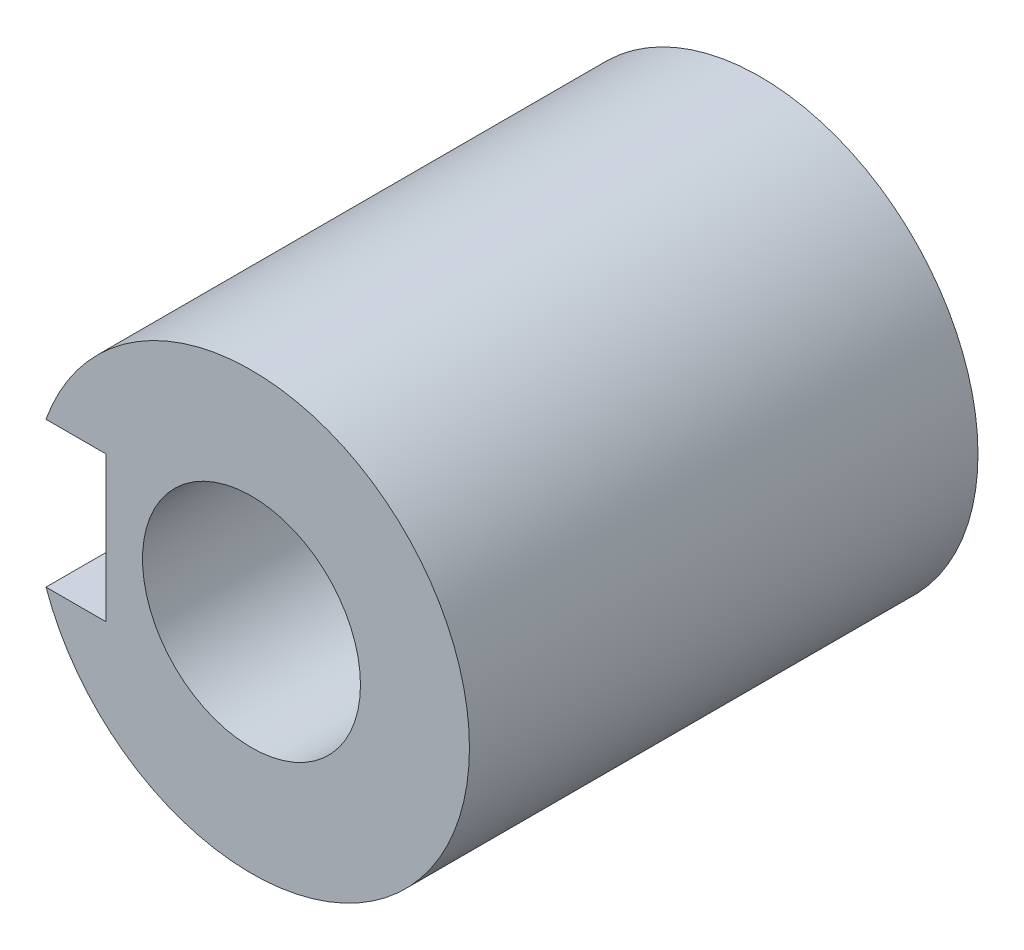
SolidWorks part; units mm, degrees
material "AISI 1020"
ref_plane "Спереди" through (0, 0, 0) normal (0, 0, 1) x (1, 0, 0)
ref_plane "Сверху" through (0, 0, 0) normal (0, 1, 0) x (1, 0, 0)
ref_plane "Справа" through (0, 0, 0) normal (1, 0, 0) x (0, 0, -1)
sketch "Эскиз1" plane through (0, 0, -1) normal (0, 0, -1) x (-1, 0, 0)
  line L0 (12, 4) -> (12, -4) construction
  line L1 (11.3137, 4) -> (8, 4)
  line L3 (11.3137, -4) -> (8, -4)
  line L4 (8, 4) -> (8, -4)
  line L5 (16, -4) -> (11.3137, -4) construction
  line L6 (11.3137, 4) -> (16, 4) construction
  arc A0 (11.3137, 4) -> (11.3137, -4) centre (0, 0) ccw
  arc A1 (11.3137, 4) -> (11.3137, -4) centre (0, 0) ccw construction
  point P6 (0, 0)
  point P15 (12, 0)
  point P17 (0, 0)
  dimension "D1" = 8
extrude "Бобышка-Вытянуть1" add sketch "Эскиз1" against normal up to surface (28 mm away)
sketch "Эскиз2" plane through (0, 0, -1) normal (0, 0, -1) x (-1, 0, 0)
  line L0 (-3.3166, 5) -> (3.3166, 5) construction
  line L1 (-3.3166, 5) -> (3.3166, 5)
  line L2 (-6, 0.6585) -> (-6, -0.6585)
  line L3 (-3.3166, -5) -> (3.3166, -5)
  line L5 (3.3166, -5) -> (-3.3166, -5) construction
  line L6 (6, 0.6585) -> (6, -0.6585)
  line L8 (-3.3166, 2) -> (3.3166, 2) construction
  line L9 (-3.3166, 2) -> (-3.3166, -2) construction
  line L10 (-3.3166, -2) -> (3.3166, -2) construction
  line L11 (3.3166, 2) -> (3.3166, -2) construction
  arc A1 (-3.3166, 5) -> (-3.3166, -5) centre (0, 0) ccw construction
  arc A2 (-3.3166, 5) -> (-6, 0.6585) centre (-3.3166, 2) ccw
  arc A3 (6, 0.6585) -> (3.3166, 5) centre (3.3166, 2) ccw
  arc A4 (3.3166, -5) -> (6, -0.6585) centre (3.3166, -2) ccw
  arc A5 (-6, -0.6585) -> (-3.3166, -5) centre (-3.3166, -2) ccw
  arc A6 (3.3166, -5) -> (3.3166, 5) centre (0, 0) ccw construction
  dimension "D1" = 6
extrude "Вырез-Вытянуть1" cut sketch "Эскиз2" against normal blind 10
sketch "Эскиз3" plane through (0, 0, 27) normal (0, 0, 1) x (1, 0, 0)
  circle A0 centre (0, 0) radius 6
extrude "Вырез-Вытянуть2" cut sketch "Эскиз3" against normal up to surface (18 mm away) up to face at (0, 0, 9)
